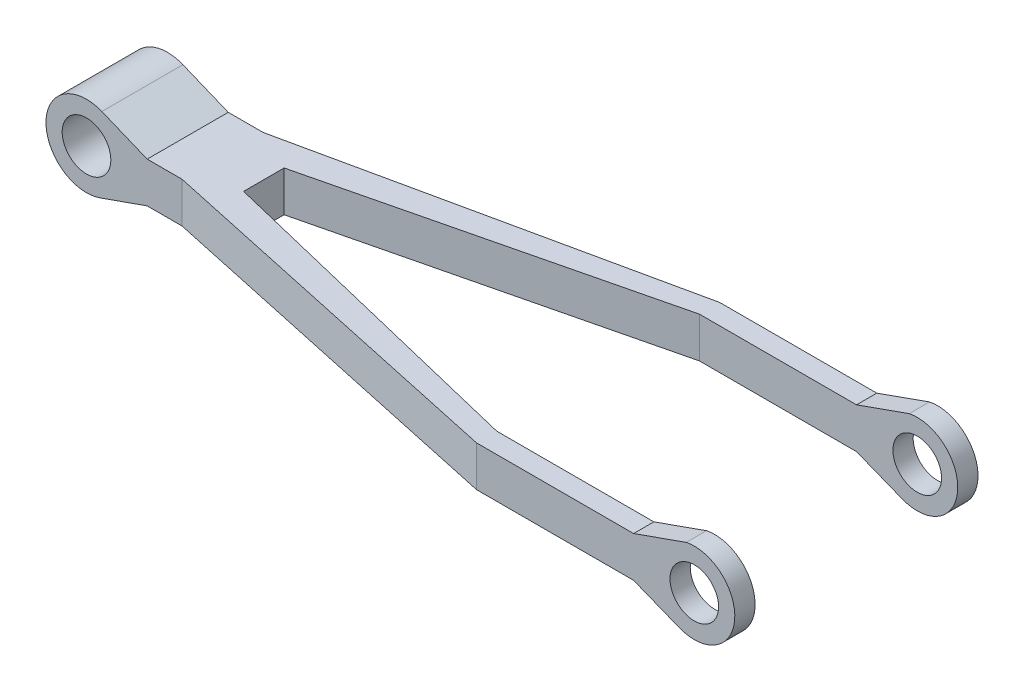
SolidWorks part; units mm, degrees
ref_plane "Front Plane" through (0, 0, 0) normal (0, 0, 1) x (1, 0, 0)
ref_plane "Top Plane" through (0, 0, 0) normal (0, 1, 0) x (1, 0, 0)
ref_plane "Right Plane" through (0, 0, 0) normal (1, 0, 0) x (0, 0, -1)
sketch "Sketch1" plane through (0, 0, 0) normal (0, 0, 1) x (1, 0, 0)
  line L0 (-349.8733, 24.6435) -> (-405.7801, 47.538)
  line L1 (350.1267, -25.3565) -> (-349.8733, -25.3565)
  line L3 (350.1267, 24.6435) -> (-349.8733, 24.6435)
  line L7 (-349.8733, -25.3565) -> (-408.1023, -45.8872)
  line L9 (0.1267, 24.6435) -> (350.1267, 24.6435) construction
  line L10 (350.1267, 24.6435) -> (415.1579, 47.7515)
  line L11 (350.1267, -25.3565) -> (406.5613, -47.7462)
  line L14 (-349.8733, 24.6435) -> (0.1267, 24.6435) construction
  arc A0 (-405.7801, 47.538) -> (-408.1023, -45.8872) centre (-424.7285, 1.2675) ccw
  arc A1 (406.5613, -47.7462) -> (401.7026, 42.9703) centre (425, -1.2703) ccw
  point P0 (0, 0)
  dimension "D4" = 100
  dimension "D5" = 100
  dimension "D1" = 700
  dimension "D2" = 50
extrude "Boss-Extrude1" add sketch "Sketch1" along normal blind 300 contours L11 A1 L10 L3 L0 A0 L7 L1
sketch "Sketch3" plane through (0, 24.6435, 0) normal (0, 1, 0) x (1, 0, 0)
  line L0 (156.3847, -275) -> (-255.9514, -175)
  line L1 (350.1267, -300) -> (-349.8733, -300) construction
  line L2 (-306.817, 0) -> (-306.817, -300) construction
  line L3 (350.1267, 0) -> (-349.8733, 0) construction
  line L4 (-306.817, -150) -> (-102.2723, -150) construction
  line L5 (-255.9514, -175) -> (-255.9514, -150)
  line L6 (-255.9514, -150) -> (-255.9514, -125)
  line L7 (-255.9514, -125) -> (156.3847, -25)
  line L8 (156.3847, -25) -> (156.3847, -150) construction
  line L9 (156.3847, -150) -> (156.3847, -275) construction
  line L10 (156.3847, -275) -> (523.2664, -275)
  line L11 (156.3847, -25) -> (646.791, -25)
  line L12 (156.3847, 0) -> (-306.817, -100)
  line L13 (156.3847, -300) -> (-306.817, -200)
  line L14 (156.3847, -300) -> (568.0939, -300)
  line L15 (568.0939, -300) -> (523.2664, -275)
  line L16 (156.3847, 0) -> (660.0038, 0)
  line L17 (660.0038, 0) -> (646.791, -25)
  line L18 (-306.817, -100) -> (-623.6055, -100)
  line L19 (-623.6055, -100) -> (-623.6055, -200)
  line L20 (-623.6055, -200) -> (-306.817, -200)
  dimension "D1" = 25
  dimension "D2" = 25
  dimension "D3" = 50
  dimension "D4" = 50
extrude "Cut-Extrude1" cut sketch "Sketch3" against normal blind 300 flip side to cut
sketch "Sketch5" plane through (0, 24.6435, 0) normal (0, 1, 0) x (1, 0, 0)
  line L0 (156.3847, -25) -> (555.9211, -25)
  line L1 (555.9211, -25) -> (555.9211, -275)
  line L2 (555.9211, -275) -> (156.3847, -275)
  line L3 (156.3847, -275) -> (-255.9514, -175) construction
  line L4 (350.1267, -275) -> (156.3847, -275) construction
  line L5 (156.3847, -25) -> (-255.9514, -125)
  line L6 (-255.9514, -125) -> (-255.9514, -175)
  line L7 (-255.9514, -175) -> (156.3847, -275)
  line L8 (-349.8733, -100) -> (-477.7336, -100)
  line L9 (-477.7336, -100) -> (-477.7336, 50.3405)
  line L10 (-477.7336, 50.3405) -> (-332.0771, 50.3405)
  line L11 (-332.0771, 50.3405) -> (-349.8733, -100)
  line L12 (-349.8733, -200) -> (-349.8733, -364.1237)
  line L13 (-349.8733, -364.1237) -> (-511.8904, -324.6474)
  line L14 (-511.8904, -324.6474) -> (-481.5194, -200)
  line L15 (-481.5194, -200) -> (-349.8733, -200)
extrude "Cut-Extrude3" cut sketch "Sketch5" along normal blind 300
sketch "Sketch6" plane through (0, 0, 200) normal (0, 0, 1) x (1, 0, 0)
  circle A0 centre (-424.7285, 1.2675) radius 30
  circle A1 centre (425, -1.2703) radius 30
  dimension "D1" = 60
extrude "Cut-Extrude4" cut sketch "Sketch6" against normal mid plane 400
